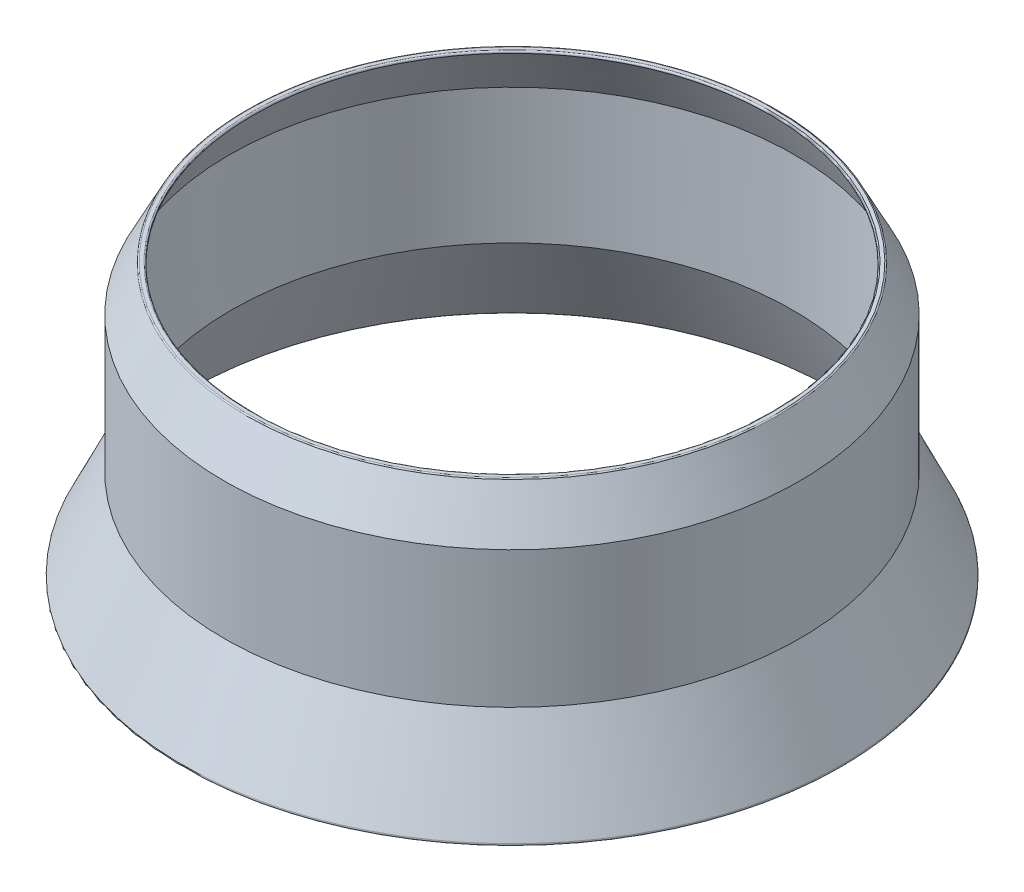
SolidWorks part; units mm, degrees
material "Tvárná litina"
ref_plane "Přední rovina" through (0, 0, 0) normal (0, 0, 1) x (1, 0, 0)
ref_plane "Horní rovina" through (0, 0, 0) normal (0, 1, 0) x (1, 0, 0)
ref_plane "Pravá rovina" through (0, 0, 0) normal (1, 0, 0) x (0, 0, -1)
sketch "Skica1" plane through (0, 0, 0) normal (0, 0, 1) x (1, 0, 0)
  line L0 (0, 0) -> (1.5402, -3)
  line L1 (1.0733, -12) -> (3.8712, -18)
  line L2 (9.5975, -12) -> (-19.9544, -12) construction
  line L3 (-3.2224, 0) -> (0, 0) construction
  line L4 (0.9692, -0.7536) -> (1.5402, -3) construction
  line L5 (1.5402, -12) -> (4.3381, -18)
  line L6 (-0.3558, -0.1827) -> (1.1844, -3.1827)
  line L7 (3.8712, -18) -> (4.3381, -18)
  line L10 (-0.3558, -0.1827) -> (-0.4496, 0)
  line L11 (0, 0) -> (-0.4496, 0)
  line L12 (-17.4496, 4.8428) -> (-17.4496, -24.7698) construction
  line L13 (1.1844, -3.1827) -> (1.0733, -12)
  line L14 (1.5402, -3) -> (1.5402, -12)
  line L15 (1.1844, -3.1827) -> (5.8256, -12.2227) construction
  line L16 (1.5402, -3) -> (6.1609, -12) construction
  line L17 (5.8256, -12.2227) -> (10.05, -17.2571) construction
  line L18 (6.1609, -12) -> (10.3564, -17) construction
  arc A1 (0, 0) -> (0.9692, -0.7536) centre (0, -1) cw construction
  dimension "D1" = 12
  dimension "D4" = 1
  dimension "D2" = 115
  dimension "D3" = 117.176
  dimension "D5" = 6
  dimension "D7" = 17
  dimension "D8" = 6
  dimension "D9" = 115
  dimension "D6" = 0.4
revolve "Rotovat1" add sketch "Skica1" angle 360 about L12
fillet "Zaoblit1" radius 0.1 4 edges at (-34.4496, 0, 0) (-34.8993, 0, 0) (-38.7705, -18, 0) (-39.2373, -18, 0)
